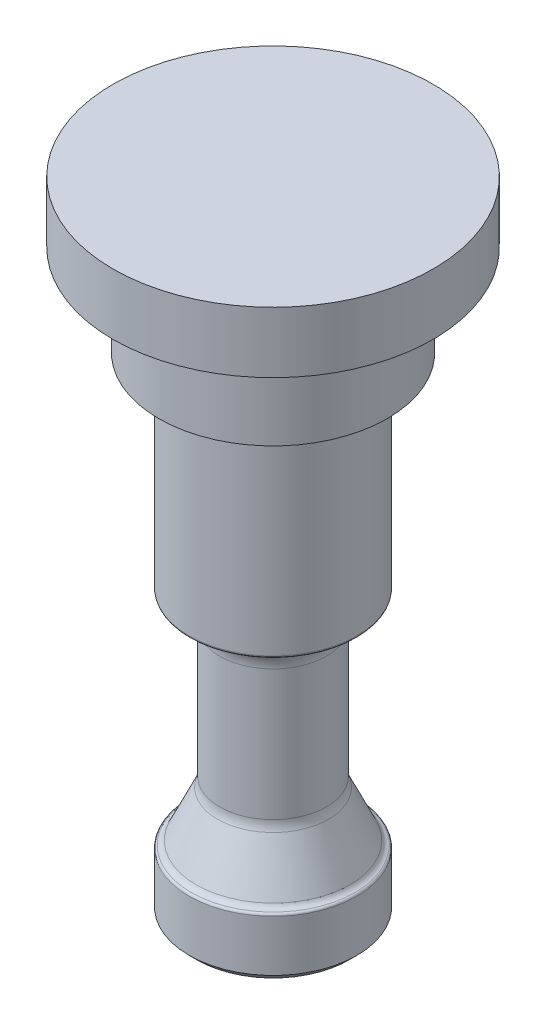
SolidWorks part; units mm, degrees
ref_plane "Front Plane" through (0, 0, 0) normal (0, 0, 1) x (1, 0, 0)
ref_plane "Top Plane" through (0, 0, 0) normal (0, 1, 0) x (1, 0, 0)
ref_plane "Right Plane" through (0, 0, 0) normal (1, 0, 0) x (0, 0, -1)
sketch "Sketch1" plane through (0, 0, 0) normal (0, 1, 0) x (1, 0, 0)
  circle A0 centre (0, 0) radius 8.7312
  dimension "D1" = 17.4625
extrude "main" add sketch "Sketch1" along normal blind 50.8
chamfer "Chamfer1" distance 0.7937 1 edges at (0, 0, 8.7312)
sketch "Sketch2" plane through (0, 0, 0) normal (1, 0, 0) x (0, 0, -1)
  line L0 (8.7312, 0.7938) -> (8.7312, 50.8) construction
  line L1 (-8.7312, 50.8) -> (-8.7312, 0.7938) construction
  line L2 (8.7312, 50.8) -> (-8.7312, 50.8) construction
  line L3 (8.7312, 0.7938) -> (8.7312, 50.8)
  line L4 (-8.7312, 50.8) -> (-8.7312, 0.7938)
  line L5 (8.7312, 50.8) -> (-8.7312, 50.8)
  line L6 (-5.7794, 11.5959) -> (-8.0119, 6.8083)
  line L8 (-8.7312, 6.35) -> (-8.7312, 29.3687)
  line L10 (-5.5562, 12.6023) -> (-5.5562, 26.1937)
  line L11 (-7.9375, 0) -> (7.9375, 0) construction
  arc A0 (-8.7312, 29.3687) -> (-5.5562, 26.1937) centre (-8.7312, 26.1937) cw
  arc A2 (-5.5562, 12.6023) -> (-5.7794, 11.5959) centre (-7.9375, 12.6023) cw
  arc A4 (-8.7312, 6.35) -> (-8.0119, 6.8083) centre (-8.7312, 7.1437) ccw
  dimension "D4" = 23.0187
  dimension "D5" = 6.2523
  dimension "D6" = 3.175
  dimension "D1" = 3.175
  dimension "D2" = 2.3812
  dimension "D3" = 0.7937
  dimension "D7" = 6.35
  dimension "D8" = 25
ref_axis "Axis1" through (0, 50.8, 0) along (0, -1, 0)
revolve "ball_channel" cut sketch "Sketch2" angle 360 about axis through (0, 50.8, 0) along (0, -1, 0)
fillet "Fillet1" radius 0.254 3 edges at (0, 29.3687, 8.7312) (0, 50.8, 8.7312) (0, 6.35, 8.7312)
sketch "Sketch6" plane through (0, 50.8, 0) normal (0, 1, 0) x (1, 0, 0)
  circle A0 centre (0, 0) radius 11.9062
  dimension "D1" = 23.8125
extrude "spring_stabilizer" add sketch "Sketch6" along normal blind 9.525
sketch "Sketch3" plane through (0, 60.325, 0) normal (0, 1, 0) x (1, 0, 0)
  circle A0 centre (0, 0) radius 16.6687
  circle A3 centre (0, 0) radius 11.9062 construction
  circle A4 centre (0, 0) radius 11.9062
  dimension "D1" = 4.7625
extrude "top_cap" add sketch "Sketch3" along normal blind 6.35
fillet "Fillet2" radius 1.27 1 edges at (0, 60.325, 11.9062)
sketch "Sketch4" [suppressed] plane through (0, 0, 0) normal (0, -1, 0) x (1, 0, 0)
  line L0 (-2.7079, 5.0327) -> (2.7079, 5.0327)
  line L1 (-2.7079, -5.0327) -> (2.7079, -5.0327)
  circle A0 centre (0, 0) radius 5.715 construction
  circle A1 centre (0, 0) radius 5.715
  circle A2 centre (0, 0) radius 5.0327 construction
  circle A3 centre (0, 0) radius 5.0327
  circle M3 centre (0, 0) radius 4.9213
  dimension "D1" = 5.4159
sketch "Sketch7" plane through (0, 0, 0) normal (0, -1, 0) x (1, 0, 0)
  circle A1 centre (0, 0) radius 2.3812
  dimension "D1" = 4.7625
extrude "Cut-Extrude1" cut sketch "Sketch7" against normal blind 19.05
ref_point "Point1"
extrude "spring_atchmnt_flat" [suppressed] cut sketch "Sketch4" against normal up to vertex contours L0 M3 | L1 M3
sketch "Sketch5" [suppressed] plane through (0, 0, 5.0327) normal (0, 0, 1) x (1, 0, 0)
  line L1 (-2.7079, 6.9053) -> (-2.7079, 0.7937) construction
  circle A0 centre (0, 3.8495) radius 1.5875
  point P7 (-2.7079, 3.8495)
  dimension "D1" = 3.175
extrude "spring_atchmnt_hole" [suppressed] cut sketch "Sketch5" against normal through all
